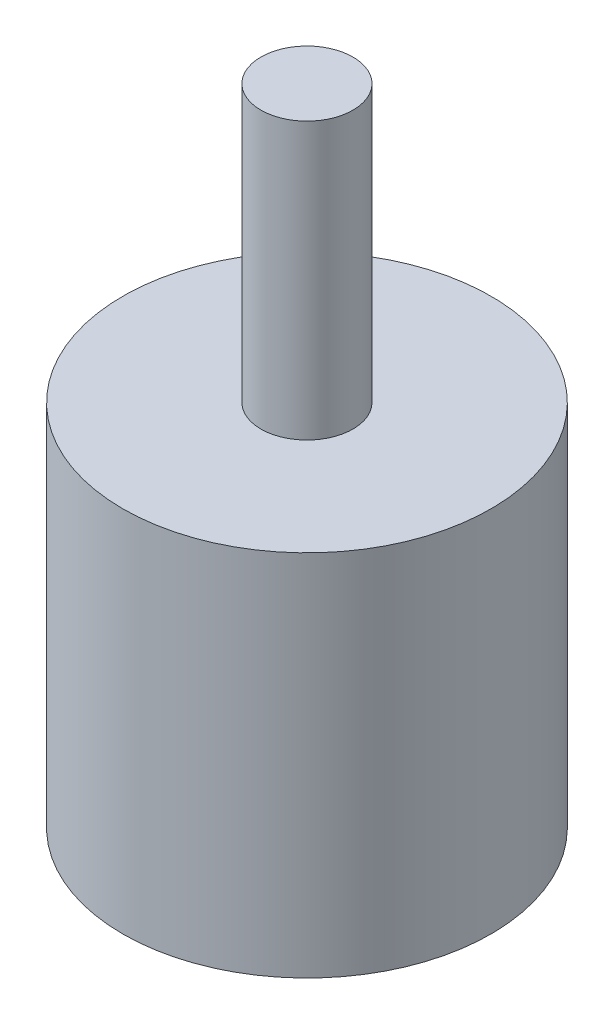
SolidWorks part; units mm, degrees
ref_plane "Front Plane" through (0, 0, 0) normal (0, 0, 1) x (1, 0, 0)
ref_plane "Top Plane" through (0, 0, 0) normal (0, 1, 0) x (1, 0, 0)
ref_plane "Right Plane" through (0, 0, 0) normal (1, 0, 0) x (0, 0, -1)
sketch "Sketch1" plane through (0, 0, 0) normal (0, 1, 0) x (1, 0, 0)
  circle A0 centre (0, 0) radius 12.7
  dimension "D1" = 25.4
extrude "Boss-Extrude1" add sketch "Sketch1" along normal blind 25.4
sketch "Sketch2" plane through (0, 25.4, 0) normal (0, 1, 0) x (1, 0, 0)
  circle A0 centre (0, 0) radius 3.175
  dimension "D1" = 6.35
extrude "Boss-Extrude2" add sketch "Sketch2" along normal blind 19.05
